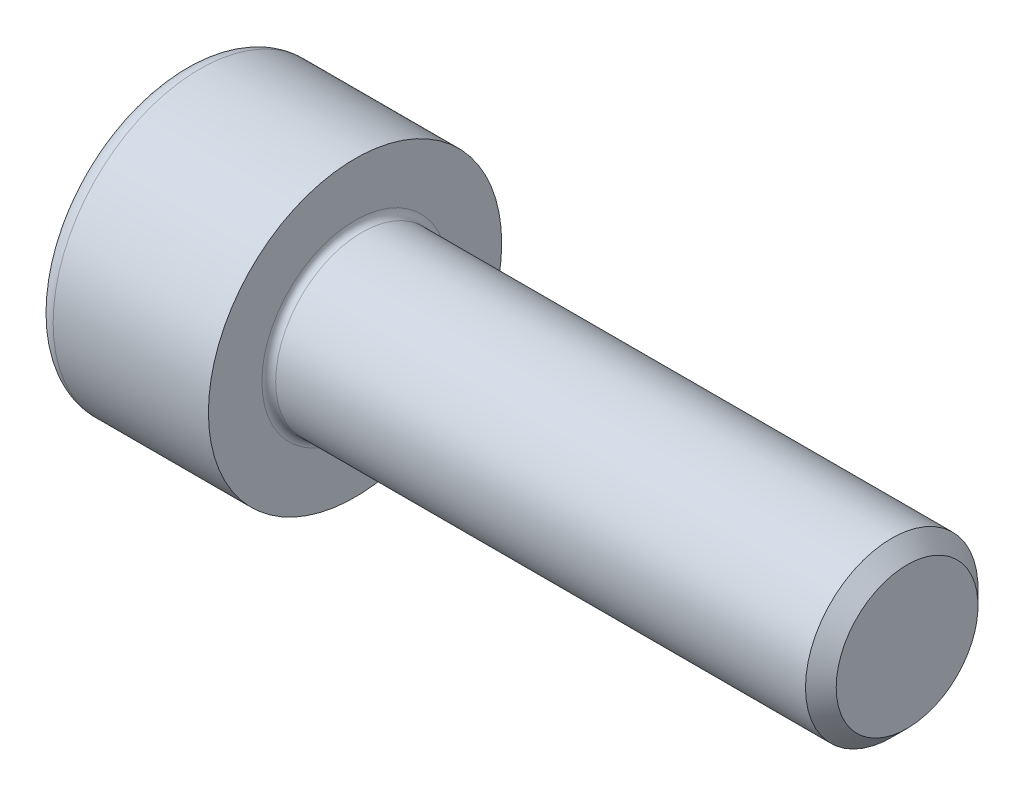
SolidWorks part; units mm, degrees
revolve "Base-Revolve" add sketch "BodySke"
sketch "BodySke" plane through (0, 0, 0) normal (0, 0, 1) x (1, 0, 0)
  line L0 (0, 0) -> (0, 4.25)
  line L1 (0, 4.25) -> (5, 4.25)
  line L2 (5, 4.25) -> (5, 2.5)
  line L3 (5, 2.5) -> (20.555, 2.5)
  line L4 (21, 2.055) -> (21, 0)
  line L5 (21, 0) -> (0, 0)
  line L6 (-31.75, 0) -> (127, 0) construction
  line L8 (21, 2.055) -> (20.555, 2.5)
  line L10 (21, -2.055) -> (20.555, -2.5) construction
  line L11 (5.8, 9.525) -> (5.8, 3.175) construction
  line L12 (5, 9.525) -> (5, 3.175) construction
  line L13 (-39, 9.525) -> (-39, 3.175) construction
  dimension "Body_ch_ang" = 45
  dimension "Thread_length" = 60
cosmetic thread "ThreadCosmetic" [suppressed]
fillet "Fillet1" radius 0.2 1 edges at (5, 0, 2.5)
fillet "Fillet2" radius 0.5 1 edges at (0, 0, 4.25)
ref_plane "Plane1" through (0, 0, 0) normal (0, 0, 1) x (1, 0, 0)
ref_plane "Plane2" through (0, 0, 0) normal (0, 1, 0) x (1, 0, 0)
ref_plane "Plane3" through (0, 0, 0) normal (1, 0, 0) x (0, 0, -1)
sketch "Sketch2" plane through (0, 0, 0) normal (0, 0, 1) x (1, 0, 0)
  line L0 (0, 2.01) -> (2.5, 2.01)
  line L1 (2.5, 2.01) -> (3.6605, 0)
  line L2 (-31.75, 0) -> (127, 0) construction
  line L3 (3.6605, 0) -> (0, 0)
  line L4 (0, 0) -> (0, 2.01)
  line L6 (0, 0) -> (47.625, 0) construction
  dimension "D2" = 60
revolve "Hex-PreBroach" cut sketch "Sketch2" angle 360 about L6
sketch "Sketch3" plane through (0, 0, 0) normal (-1, 0, 0) x (0, 0.5, 0.866)
  line L0 (1.1605, 2.01) -> (-1.1605, 2.01)
  line L1 (-1.1605, 2.01) -> (-2.3209, 0)
  line L2 (1.1605, 2.01) -> (2.3209, 0)
  line L3 (1.1605, -2.01) -> (2.3209, 0)
  line L4 (1.1605, -2.01) -> (-1.1605, -2.01)
  line L5 (-1.1605, -2.01) -> (-2.3209, 0)
extrude "Hex" cut sketch "Sketch3" against normal blind 2.5
sketch "ThdSchSke" plane through (0, 0, 0) normal (0, 0, 1) x (1, 0, 0)
  line L0 (7.4, -2.055) -> (7.0884, -2.5)
  line L1 (7.4, -2.055) -> (7.7116, -2.5)
  line L2 (7.7116, -2.5) -> (7.7116, -3.125)
  line L3 (-3.175, 0) -> (5.1513, 0) construction
  line L4 (0, 3.75) -> (0, -3.75) construction
  line L5 (7.7116, -3.125) -> (7.0884, -3.125)
  line L6 (7.0884, -3.125) -> (7.0884, -2.5)
revolve "ThreadSchematic" [suppressed] cut sketch "ThdSchSke" angle 360 about L3
pattern_linear "ThdSchPat" [suppressed]
equation "\"D2@Sketch3\" = \"Hex_size@Sketch3\" / 2"
equation "\"D1@Sketch3\" = \"Hex_size@Sketch3\" / 2"
equation "\"D1@Sketch2\" = \"Hex_size@Sketch3\" / 2"
equation "\"Thread_minor@ThreadCosmetic\"  =  \"Minor_dia@BodySke\""
equation "\"Depth@Sketch2\" =  \"Key_eng@Hex\""
equation "\"Thread_length@ThreadCosmetic\" = ((sgn( (\"Length@BodySke\" - \"Advance@BodySke\" * 3.0) - \"Thread_nom@BodySke\" )-1)*( (\"Length@BodySke\" - \"Advance@BodySke\" * 3.0) - \"Thread_nom@BodySke\" ))/-2+ \"Thread_nom@BodySke\""
equation "\"Thread_minor@ThdSchSke\" = \"Minor_dia@BodySke\""
equation "\"Diameter@ThdSchSke\" = \"Diameter@BodySke\""
equation "\"Overcut@ThdSchSke\" = \"Diameter@BodySke\" * 1.25"
equation "\"Start@ThdSchSke\" = \"Head_ht@BodySke\" + \"Length@BodySke\" - \"Thread_length@ThreadCosmetic\"  '---Non-countersunk---"
equation "\"Num_threads@ThdSchPat\" = int( \"Thread_length@ThreadCosmetic\" / \"Advance@BodySke\" + 0.999 )  + 1"
equation "\"Advance@ThdSchPat\" = \"Thread_length@ThreadCosmetic\" /  (\"Num_threads@ThdSchPat\" - 1) 'relax it"
equation "\"Num_threads@ThdSchPat\" = \"Num_threads@ThdSchPat\" - sgn( \"Num_threads@ThdSchPat\" - 1) '---chamfered tips only---"
